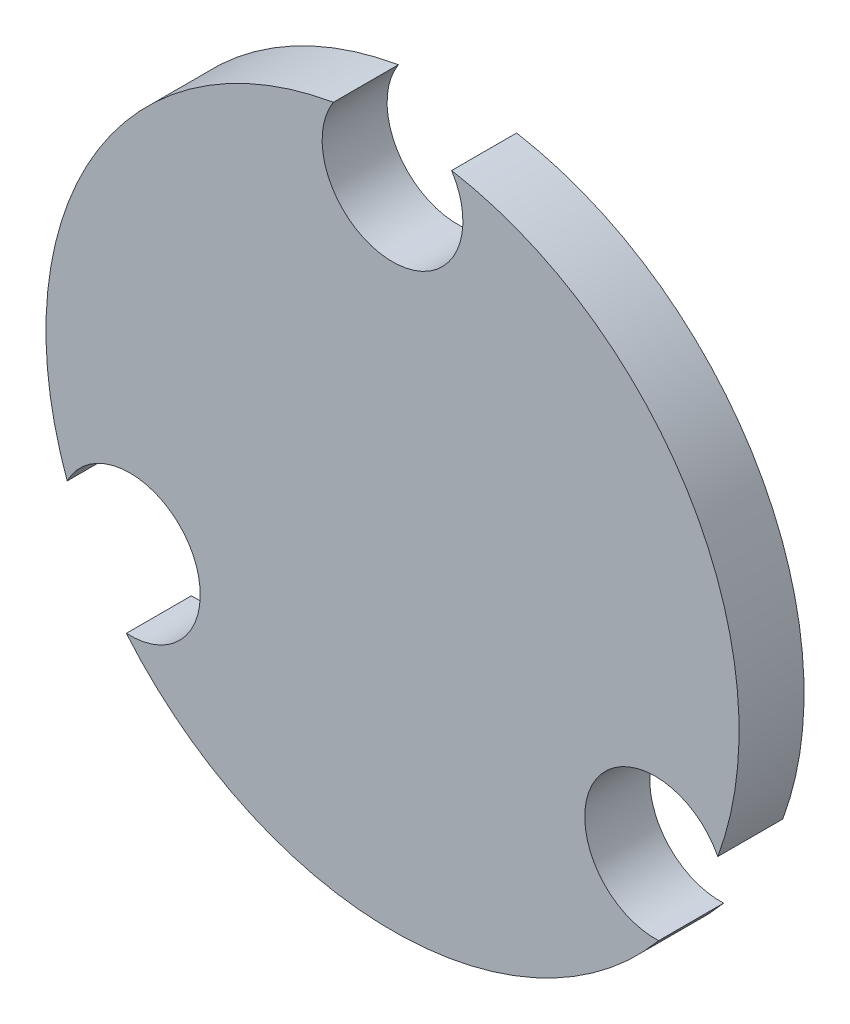
SolidWorks part; units mm, degrees
ref_plane "Plan de face" through (0, 0, 0) normal (0, 0, 1) x (1, 0, 0)
ref_plane "Plan de dessus" through (0, 0, 0) normal (0, 1, 0) x (1, 0, 0)
ref_plane "Plan de droite" through (0, 0, 0) normal (1, 0, 0) x (0, 0, -1)
sketch "Esquisse1" plane through (0, 0, 0) normal (0, 0, 1) x (1, 0, 0)
  line L1 (-10.6244, -7.0011) -> (-8.8744, -7.0011) construction
  line L2 (12.125, -7.0011) -> (10.4994, -4.1854) construction
  line L3 (-10.4994, -4.1854) -> (-12.125, -7.0011) construction
  arc A0 (-12.2881, -10.247) -> (12.2891, -10.2458) centre (0, 0) ccw
  arc A30 (15.0177, -5.5198) -> (12.2891, -10.2458) centre (12.1244, -7) ccw
  arc A31 (-12.2881, -10.247) -> (-15.0177, -5.5197) centre (-12.125, -7.0011) ccw
  arc A32 (-2.7286, 15.7656) -> (2.7286, 15.7656) centre (0, 14) ccw
  arc A33 (-2.7286, 15.7656) -> (-15.0177, -5.5197) centre (0, 0) ccw
  arc A34 (15.0177, -5.5198) -> (2.7286, 15.7656) centre (0, 0) ccw
  point P31 (0, 0)
  dimension "D1" = 32
  dimension "D4" = 6.5
  dimension "D5" = 6.5
  dimension "D8" = 6.5
  dimension "D12" = 24.25
  dimension "D13" = 24.25
extrude "Boss.-Extru.2" add sketch "Esquisse1" along normal blind 3
